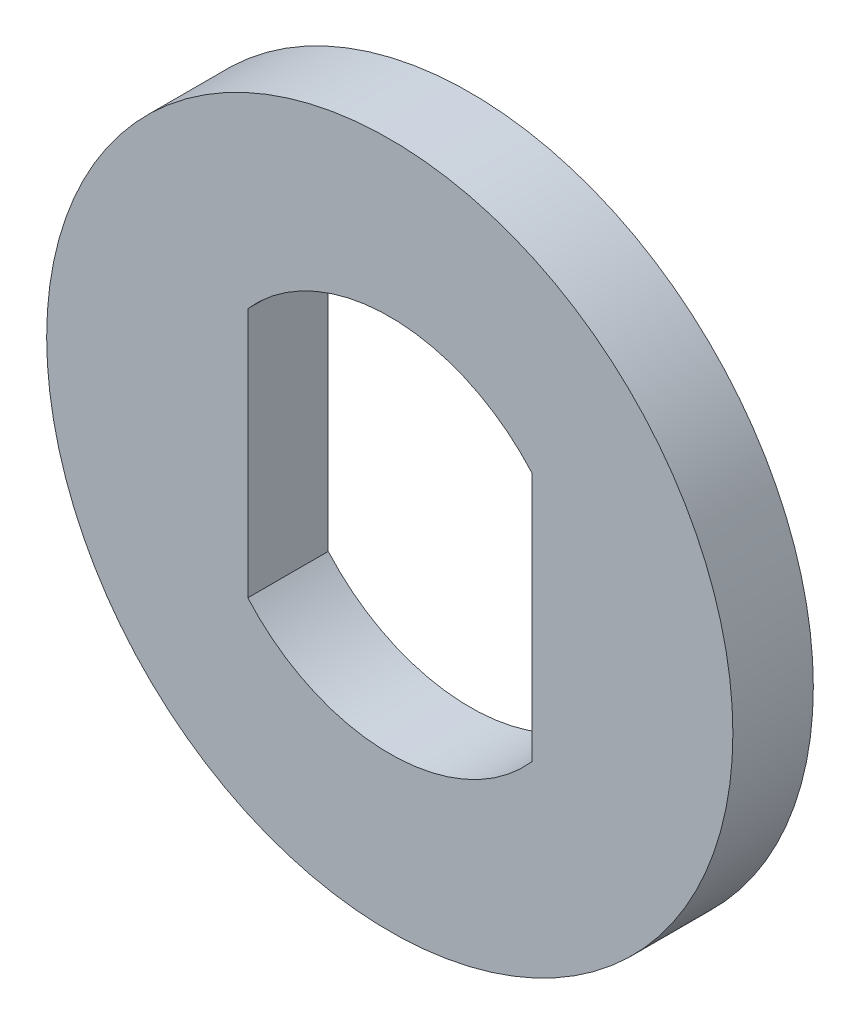
SolidWorks part; units mm, degrees
ref_plane "Plan de face" through (0, 0, 0) normal (0, 0, 1) x (1, 0, 0)
ref_plane "Plan de dessus" through (0, 0, 0) normal (0, 1, 0) x (1, 0, 0)
ref_plane "Plan de droite" through (0, 0, 0) normal (1, 0, 0) x (0, 0, -1)
sketch "Esquisse1" plane through (0, 0, 0) normal (0, 0, 1) x (1, 0, 0)
  line L0 (0, 0) -> (13.1748, 0) construction
  line L1 (0, 0) -> (0, 13.0313) construction
  line L4 (-3, 2.6458) -> (-3, -2.6458)
  line L6 (3, 2.6458) -> (3, -2.6458)
  circle A0 centre (0, 0) radius 7.25
  arc A3 (3, 2.6458) -> (-3, 2.6458) centre (0, 0) ccw
  arc A4 (-3, -2.6458) -> (3, -2.6458) centre (0, 0) ccw
  dimension "D2" = 8
  dimension "D3" = 14.5
  dimension "D1" = 6
extrude "Extrusion1" add sketch "Esquisse1" along normal mid plane 1.7
